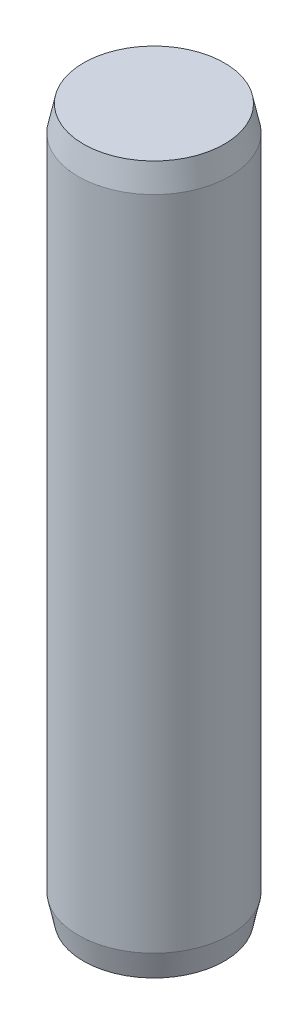
SolidWorks part; units mm, degrees
ref_plane "Front Plane" through (0, 0, 0) normal (0, 0, 1) x (1, 0, 0)
ref_plane "Top Plane" through (0, 0, 0) normal (0, 1, 0) x (1, 0, 0)
ref_plane "Right Plane" through (0, 0, 0) normal (1, 0, 0) x (0, 0, -1)
sketch "Sketch1" plane through (0, 0, 0) normal (0, 1, 0) x (1, 0, 0)
  circle A0 centre (0, 0) radius 1.5
  dimension "D1" = 3
extrude "Boss-Extrude1" add sketch "Sketch1" along normal blind 14
chamfer "Chamfer1" distance 0.5 angle 12 1 edges at (0, 14, 1.5)
chamfer "Chamfer2" distance 0.5 angle 12 1 edges at (0, 0, 1.5)
